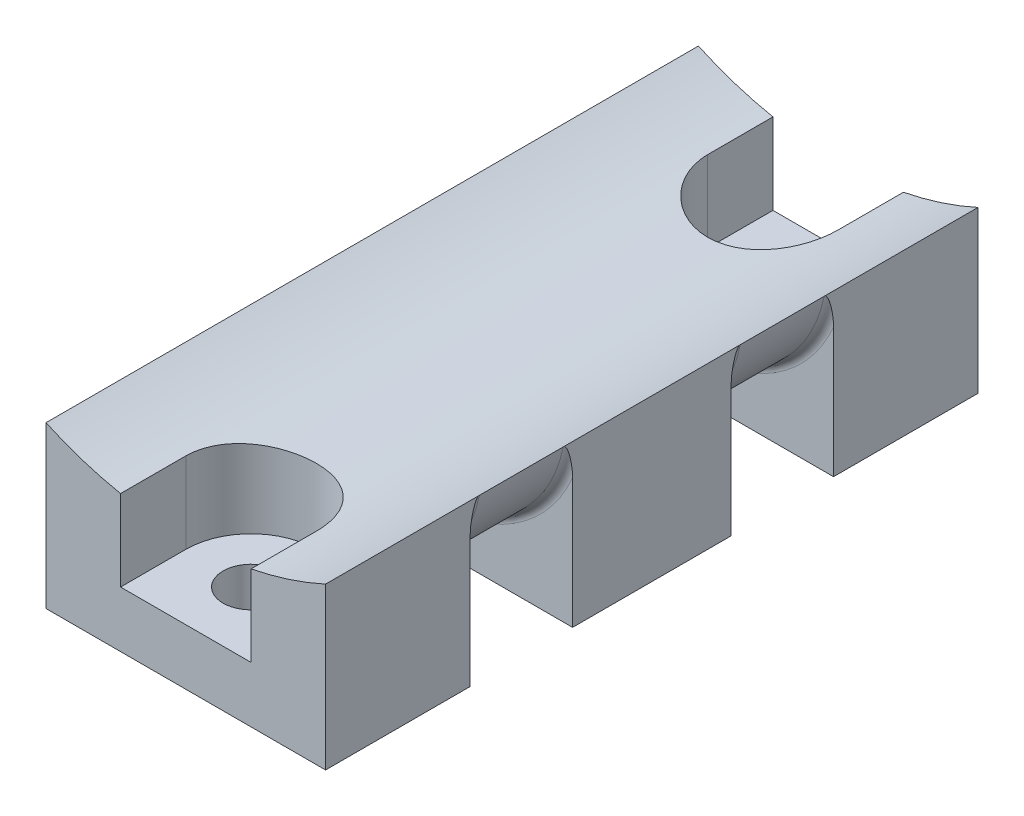
SolidWorks part; units mm, degrees
ref_plane "Front Plane" through (0, 0, 0) normal (0, 0, 1) x (1, 0, 0)
ref_plane "Top Plane" through (0, 0, 0) normal (0, 1, 0) x (1, 0, 0)
ref_plane "Right Plane" through (0, 0, 0) normal (1, 0, 0) x (0, 0, -1)
sketch "Sketch1" plane through (0, 0, 0) normal (0, 0, 1) x (1, 0, 0)
  line L1 (-7.5, 2.5623) -> (7.5, 2.5623)
  line L2 (-7.5, 2.5623) -> (-7.5, 11.1992)
  line L4 (7.5, 2.5623) -> (7.5, 11.1992)
  arc A0 (-7.5, 11.1992) -> (7.5, 11.1992) centre (0, 27.5623) ccw
  dimension "D4" = 36
  dimension "D2" = 7.5
  dimension "D5" = 25
extrude "Boss-Extrude1" add sketch "Sketch1" along normal blind 35
sketch "Sketch2" plane through (0, 2.5623, 0) normal (0, -1, 0) x (1, 0, 0)
  line L0 (0, 35) -> (0, 0) construction
  line L1 (-7.5, 35) -> (7.5, 35) construction
  circle A0 centre (0, 31.5) radius 3.5
  circle A1 centre (0, 3.5) radius 3.5
  circle A2 centre (0, 17.5) radius 3.5
  dimension "D1" = 7
  dimension "D2" = 7
  dimension "D3" = 7
  dimension "D4" = 14
  dimension "D5" = 14
ref_plane "Plane1" through (0, 5.5623, 0) normal (0, -1, 0) x (-1, 0, 0)
sketch "Sketch3" plane through (0, 5.5623, 0) normal (0, -1, 0) x (-1, 0, 0)
  line L0 (-3.5, -3.5) -> (-3.5, 2.9199)
  line L1 (-3.5, 2.9199) -> (3.5, 2.9199)
  line L2 (3.5, 2.9199) -> (3.5, -3.5)
  line L6 (3.5, -31.5) -> (3.5, -38.1896)
  line L7 (3.5, -38.1896) -> (-3.5, -38.1896)
  line L8 (-3.5, -38.1896) -> (-3.5, -31.5)
  circle A0 centre (0, -3.5) radius 3.5 construction
  circle A2 centre (0, -31.5) radius 3.5 construction
  arc A3 (-3.5, -3.5) -> (3.5, -3.5) centre (0, -3.5) ccw
  arc A5 (3.5, -31.5) -> (-3.5, -31.5) centre (0, -31.5) ccw
extrude "Cut-Extrude1" cut sketch "Sketch3" against normal blind 30
ref_plane "Plane2" through (0, 0, 7.75) normal (0, 0, 1) x (1, 0, 0)
sketch "Sketch5" plane through (0, 0, 7.75) normal (0, 0, 1) x (1, 0, 0)
  line L0 (0, 5.0623) -> (0, 2.5623) construction
  line L1 (-7.5, 2.5623) -> (7.5, 2.5623) construction
  line L2 (-7.5, 11.1992) -> (-7.5, 2.5623) construction
  line L3 (7.5, 2.5623) -> (7.5, 11.1992) construction
  line L4 (-7.5, 11.1992) -> (-7.5, 2.5623)
  line L5 (-7.5, 2.5623) -> (7.5, 2.5623)
  line L6 (7.5, 2.5623) -> (7.5, 11.1992)
  arc A1 (-7.5, 11.1992) -> (7.5, 11.1992) centre (0, 12.7137) ccw
extrude "Cut-Extrude3" cut sketch "Sketch5" along normal blind 5.5
ref_plane "Plane3" through (0, 0, 27.25) normal (0, 0, 1) x (1, 0, 0)
sketch "Sketch6" plane through (0, 0, 27.25) normal (0, 0, 1) x (1, 0, 0)
  line L3 (-7.5, 11.1992) -> (-7.5, 2.5623)
  line L4 (-7.5, 2.5623) -> (7.5, 2.5623)
  line L5 (7.5, 2.5623) -> (7.5, 11.1992)
  line L6 (-7.5, 11.1992) -> (-7.5, 2.5623)
  line L7 (-7.5, 2.5623) -> (7.5, 2.5623)
  line L8 (7.5, 2.5623) -> (7.5, 11.1992)
  arc A1 (-7.5, 11.1992) -> (7.5, 11.1992) centre (0, 12.7137) ccw
  arc A2 (-7.5, 11.1992) -> (7.5, 11.1992) centre (0, 12.7137) ccw
  dimension "D1" = 0
extrude "Cut-Extrude4" cut sketch "Sketch6" against normal blind 5.5
sketch "Sketch7" plane through (0, 5.5623, 0) normal (0, 1, 0) x (1, 0, 0)
  circle A0 centre (0, -3.5) radius 1.5
  circle A1 centre (0, -31.5) radius 1.5
  dimension "D1" = 3
  dimension "D2" = 3
extrude "Cut-Extrude5" cut sketch "Sketch7" against normal through all
fillet "Fillet1" radius 0.5 4 edges at (0, 5.0623, 21.75) (0, 5.0623, 27.25) (0, 5.0623, 13.25) (0, 5.0623, 7.75)
